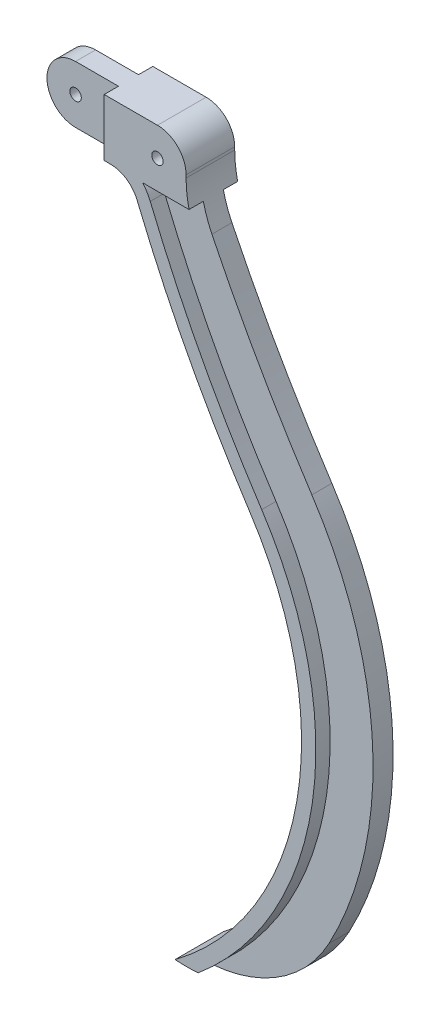
SolidWorks part; units mm, degrees
ref_plane "Alzado" through (0, 0, 0) normal (0, 0, 1) x (1, 0, 0)
ref_plane "Planta" through (0, 0, 0) normal (0, 1, 0) x (1, 0, 0)
ref_plane "Vista lateral" through (0, 0, 0) normal (1, 0, 0) x (0, 0, -1)
sketch "Croquis1" plane through (0, 0, 0) normal (0, 0, 1) x (1, 0, 0)
  line L0 (0, 161.3613) -> (59.639, 161.3613)
  line L1 (0, 141.3613) -> (0, 161.3613)
  line L7 (69.639, 151.3613) -> (69.639, 150.371)
  line L11 (43.2364, 141.3613) -> (0, 141.3613)
  arc A0 (114.5914, -61.3907) -> (65.787, -88.1593) centre (69.639, -37.3082) cw
  arc A1 (65.787, -88.1593) -> (91.8968, 60.4564) centre (0, 0) ccw
  arc A3 (91.8968, 60.4564) -> (52.4893, 135.1541) centre (458.2789, 301.4889) cw
  arc A4 (114.5914, -61.3907) -> (108.6053, 71.4484) centre (0, 0) ccw
  arc A5 (108.6053, 71.4484) -> (73.6621, 132.8878) centre (564.7594, 371.5395) cw
  arc A6 (69.639, 151.3613) -> (59.639, 161.3613) centre (59.639, 151.3613) ccw
  arc A7 (73.6621, 132.8878) -> (69.639, 150.371) centre (109.639, 150.371) cw
  arc A8 (52.4893, 135.1541) -> (43.2364, 141.3613) centre (43.2364, 131.3613) ccw
  circle A9 centre (59.639, 151.3613) radius 2
  dimension "D1" = 10
  dimension "D2" = 40
  dimension "D3" = 10
  dimension "D4" = 4
extrude "Saliente-Extruir1" add sketch "Croquis1" along normal blind 7
sketch "Croquis2" plane through (0, 0, 7) normal (0, 0, 1) x (1, 0, 0)
  line L0 (43.2364, 141.3613) -> (54.4168, 141.3613)
  line L1 (43.2364, 141.3613) -> (54.4168, 141.3613)
  arc A0 (65.787, -88.1593) -> (73.881, -88.1283) centre (69.639, -37.3082) ccw
  arc A3 (65.787, -88.1593) -> (114.5914, -61.3907) centre (69.639, -37.3082) ccw construction
  arc A4 (57.1157, 137.0505) -> (96.074, 63.2044) centre (458.2789, 301.4889) ccw
  arc A5 (68.7773, -92.1666) -> (96.074, 63.2044) centre (0, 0) ccw
  arc A6 (57.1157, 137.0505) -> (96.074, 63.2044) centre (458.2789, 301.4889) ccw
  arc A7 (73.881, -88.1283) -> (96.074, 63.2044) centre (0, 0) ccw
  arc A8 (57.1157, 137.0505) -> (43.2364, 146.3613) centre (43.2364, 131.3613) ccw
  arc A9 (57.1157, 137.0505) -> (54.4168, 141.3613) centre (43.2364, 131.3613) ccw
  arc A10 (65.787, -88.1593) -> (91.8968, 60.4564) centre (0, 0) ccw construction
  arc A11 (65.787, -88.1593) -> (91.8968, 60.4564) centre (0, 0) ccw
  arc A12 (91.8968, 60.4564) -> (52.4893, 135.1541) centre (458.2789, 301.4889) cw
  arc A13 (43.2364, 141.3613) -> (52.4893, 135.1541) centre (43.2364, 131.3613) cw
  arc M4 (52.4893, 135.1541) -> (91.8968, 60.4564) centre (458.2789, 301.4889) ccw
  arc M5 (91.8968, 60.4564) -> (65.787, -88.1593) centre (0, 0) cw
  arc M6 (65.787, -88.1593) -> (114.5914, -61.3907) centre (69.639, -37.3082) ccw
  arc M15 (43.2364, 141.3613) -> (52.4893, 135.1541) centre (43.2364, 131.3613) cw
  dimension "D1" = 5
  dimension "D2" = 5
extrude "Saliente-Extruir2" add sketch "Croquis2" along normal blind 5 contours A6 A9 L0 A7 M15 M4 M5 M6
sketch "Croquis3" plane through (0, 0, 0) normal (0, 0, -1) x (-1, 0, 0)
  line L0 (-43.2364, 141.3613) -> (-54.4168, 141.3613)
  arc A0 (-43.2364, 141.3613) -> (-52.4893, 135.1541) centre (-43.2364, 131.3613) ccw
  arc A1 (-52.4893, 135.1541) -> (-91.8968, 60.4564) centre (-458.2789, 301.4889) cw
  arc A2 (-73.881, -88.1283) -> (-65.787, -88.1593) centre (-69.639, -37.3082) ccw
  arc A3 (-65.787, -88.1593) -> (-91.8968, 60.4564) centre (0, 0) cw
  arc A9 (-96.074, 63.2044) -> (-68.7773, -92.1666) centre (0, 0) ccw
  arc A10 (-96.074, 63.2044) -> (-57.1157, 137.0505) centre (-458.2789, 301.4889) ccw
  arc A11 (-43.2364, 146.3613) -> (-57.1157, 137.0505) centre (-43.2364, 131.3613) ccw
  arc A12 (-96.074, 63.2044) -> (-73.881, -88.1283) centre (0, 0) ccw
  arc A13 (-96.074, 63.2044) -> (-57.1157, 137.0505) centre (-458.2789, 301.4889) ccw
  arc A14 (-54.4168, 141.3613) -> (-57.1157, 137.0505) centre (-43.2364, 131.3613) ccw
  dimension "D1" = 5
extrude "Saliente-Extruir3" add sketch "Croquis3" along normal blind 5 separate body
sketch "Croquis4" plane through (0, 0, 7) normal (0, 0, 1) x (1, 0, 0)
  line L0 (69.639, 151.3613) -> (69.639, 150.371)
  line L1 (54.4168, 141.3613) -> (0, 141.3613)
  line L2 (0, 141.3613) -> (0, 161.3613)
  line L3 (0, 161.3613) -> (59.639, 161.3613)
  line L4 (54.4168, 141.3613) -> (70.6669, 141.3613)
  arc A1 (59.639, 161.3613) -> (69.639, 151.3613) centre (59.639, 151.3613) cw
  arc A2 (70.6669, 141.3613) -> (69.639, 150.371) centre (109.639, 150.371) cw
extrude "Saliente-Extruir4" add sketch "Croquis4" along normal blind 5
sketch "Croquis6" plane through (0, 0, 0) normal (0, 0, -1) x (-1, 0, 0)
  circle A0 centre (-59.639, 151.3613) radius 2
extrude "Cortar-Extruir1" cut sketch "Croquis6" against normal blind 20
sketch "Croquis7" plane through (0, 0, 0) normal (0, 0, -1) x (-1, 0, 0)
  line L0 (0, 161.3613) -> (-59.639, 161.3613)
  line L1 (0, 161.3613) -> (0, 141.3613)
  line L2 (0, 141.3613) -> (-54.4168, 141.3613)
  line L3 (-54.4168, 141.3613) -> (-70.6669, 141.3613)
  line L4 (-69.639, 151.3613) -> (-69.639, 150.371)
  arc A0 (-59.639, 161.3613) -> (-69.639, 151.3613) centre (-59.639, 151.3613) ccw
  arc A1 (-69.639, 150.371) -> (-70.6669, 141.3613) centre (-109.639, 150.371) cw
extrude "Saliente-Extruir5" add sketch "Croquis7" along normal blind 5
sketch "Croquis8" plane through (0, 0, 12) normal (0, 0, 1) x (1, 0, 0)
  circle A0 centre (59.639, 151.3613) radius 2
extrude "Cortar-Extruir3" cut sketch "Croquis8" against normal blind 20
sketch "Croquis9" plane through (0, 0, 12) normal (0, 0, 1) x (1, 0, 0)
  line L0 (0, 161.3613) -> (0, 174.3164)
  line L1 (0, 174.3164) -> (75.3432, 174.3164)
  line L2 (37.6716, 161.3613) -> (37.6716, 141.3613)
  line L3 (37.6716, 161.3613) -> (26.0064, 161.3613)
  line L4 (59.639, 161.3613) -> (0, 161.3613) construction
  line L5 (37.6716, 141.3613) -> (26.0064, 141.3613)
  line L6 (0, 141.3613) -> (43.2364, 141.3613) construction
  line L7 (26.0064, 161.3613) -> (0, 161.3613)
  line L8 (0, 141.3613) -> (26.0064, 141.3613)
  line L9 (26.0064, 141.3613) -> (37.6716, 141.3613)
  line L10 (26.0064, 161.3613) -> (37.6716, 161.3613)
  line L11 (26.0064, 141.3613) -> (37.6716, 141.3613)
  circle A0 centre (26.0064, 151.3613) radius 2
  arc A1 (26.0064, 161.3613) -> (26.0064, 141.3613) centre (26.0064, 151.3613) ccw
  line M8 (59.639, 161.3613) -> (0, 161.3613)
  line M9 (0, 161.3613) -> (0, 141.3613)
  line M10 (0, 141.3613) -> (43.2364, 141.3613)
  dimension "D1" = 4
extrude "Cortar-Extruir4" cut sketch "Croquis9" against normal blind 20 contours A1 M8 M9 M10
sketch "Croquis10" plane through (0, 0, 12) normal (0, 0, 1) x (1, 0, 0)
  line L0 (26.0064, 161.3613) -> (26.0064, 141.3613)
  line L2 (41.0064, 151.3613) -> (41.0064, 161.3613)
  line L3 (59.639, 161.3613) -> (26.0064, 161.3613) construction
  line L4 (41.0064, 161.3613) -> (41.0064, 141.3613)
  line L5 (26.0064, 141.3613) -> (43.2364, 141.3613) construction
  line L6 (41.0064, 161.3613) -> (26.0064, 161.3613)
  line L7 (41.0064, 141.3613) -> (26.0064, 141.3613)
  circle A0 centre (26.0064, 151.3613) radius 2
  arc A1 (26.0064, 141.3613) -> (26.0064, 161.3613) centre (26.0064, 151.3613) cw
  line M2 (59.639, 161.3613) -> (26.0064, 161.3613)
  arc M3 (26.0064, 161.3613) -> (26.0064, 141.3613) centre (26.0064, 151.3613) ccw
  line M4 (26.0064, 141.3613) -> (43.2364, 141.3613)
  dimension "D1" = 4
  dimension "D2" = 15
extrude "Cortar-Extruir5" cut sketch "Croquis10" against normal blind 5 contours A0 L0 M3 | A0 L0 L4 L2 M4 M2
sketch "Croquis11" plane through (0, 161.3613, 0) normal (0, 1, 0) x (1, 0, 0)
  line L0 (41.0064, -7) -> (41.0064, 5)
  line L1 (26.0064, 5) -> (59.639, 5) construction
sketch "Croquis12" plane through (0, 0, -5) normal (0, 0, -1) x (-1, 0, 0)
  line L0 (-41.0064, 161.3613) -> (-41.0064, 141.3613)
  line L1 (-26.0064, 161.3613) -> (-26.0064, 141.3613)
  line L2 (-41.0064, 161.3613) -> (-26.0064, 161.3613)
  line L3 (-41.0064, 141.3613) -> (-26.0064, 141.3613)
  circle A0 centre (-26.0064, 151.3613) radius 2
  arc A1 (-26.0064, 141.3613) -> (-26.0064, 161.3613) centre (-26.0064, 151.3613) ccw
  line M2 (-43.2364, 141.3613) -> (-26.0064, 141.3613)
  arc M3 (-26.0064, 141.3613) -> (-26.0064, 161.3613) centre (-26.0064, 151.3613) ccw
  line M4 (-26.0064, 161.3613) -> (-59.639, 161.3613)
  dimension "D1" = 4
extrude "Cortar-Extruir6" cut sketch "Croquis12" against normal blind 5 contours A0 L1 L0 M4 M2 | A0 L1 M3
sketch "Croquis13" plane through (0, 0, -5) normal (0, 0, -1) x (-1, 0, 0)
  circle A0 centre (-26.0064, 151.3613) radius 2
extrude "Cortar-Extruir7" cut sketch "Croquis13" against normal blind 45
